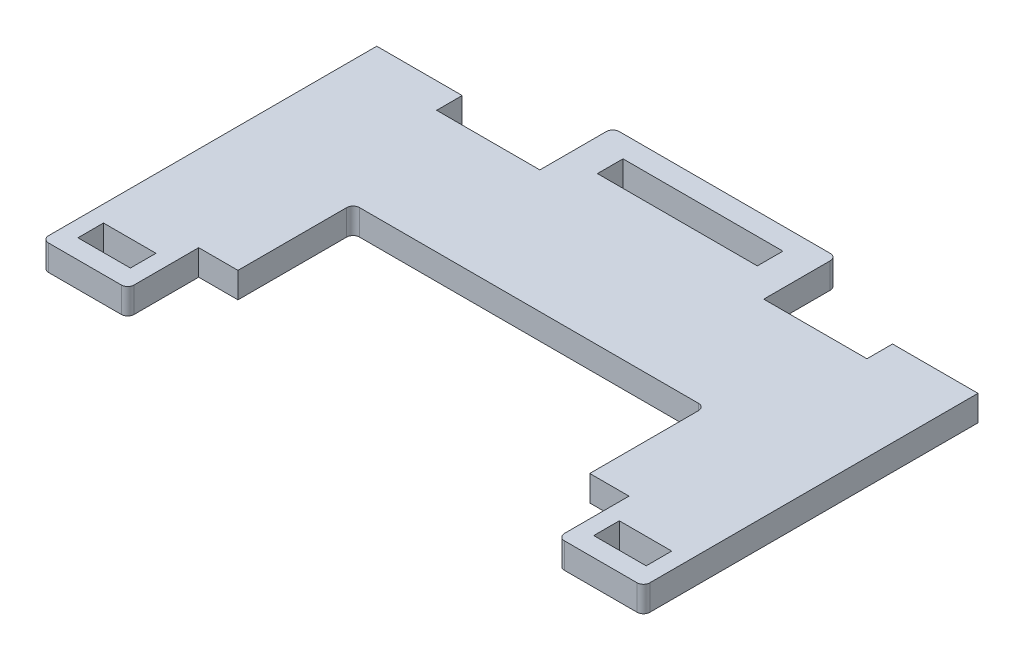
SolidWorks part; units mm, degrees
material "Oak"
ref_plane "Front Plane" through (0, 0, 0) normal (0, 0, 1) x (1, 0, 0)
ref_plane "Top Plane" through (0, 0, 0) normal (0, 1, 0) x (1, 0, 0)
ref_plane "Right Plane" through (0, 0, 0) normal (1, 0, 0) x (0, 0, -1)
sketch "Sketch1" plane through (0, 0, 0) normal (0, 1, 0) x (1, 0, 0)
  line L0 (0, 0) -> (0, 52.3)
  line L1 (0, 52.3) -> (13.36, 52.3)
  line L2 (13.36, 52.3) -> (13.36, 48.3)
  line L3 (13.36, 48.3) -> (29.5, 48.3)
  line L4 (29.5, 48.3) -> (29.5, 59.7)
  line L5 (29.5, 59.7) -> (47, 59.7)
  line L6 (47, 59.7) -> (47, 29.1)
  line L7 (47, 29.1) -> (19.5, 29.1)
  line L8 (19.5, 29.1) -> (19.5, 11.1)
  line L9 (19.5, 11.1) -> (13.36, 11.1)
  line L10 (13.36, 11.1) -> (13.36, 0)
  line L11 (13.36, 0) -> (0, 0)
  line L13 (2.58, 3) -> (10.78, 3)
  line L14 (2.58, 3) -> (2.58, 7)
  line L15 (2.58, 7) -> (10.78, 7)
  line L16 (10.78, 3) -> (10.78, 7)
  line L17 (47, 56.3) -> (34.5, 56.3)
  line L18 (47, 56.3) -> (47, 52.3)
  line L19 (47, 52.3) -> (34.5, 52.3)
  line L20 (34.5, 56.3) -> (34.5, 52.3)
  point P6 (6.68, 3)
  point P18 (6.68, 0)
  dimension "D1" = 47
  dimension "D2" = 52.3
  dimension "D3" = 4
  dimension "D4" = 13.36
  dimension "D5" = 27.5
  dimension "D6" = 11.1
  dimension "D7" = 18
  dimension "D8" = 17.5
  dimension "D9" = 11.4
  dimension "D10" = 8.2
  dimension "D11" = 4
  dimension "D12" = 3
  dimension "D13" = 5
  dimension "D14" = 4
  dimension "D15" = 3.4
extrude "Boss-Extrude1" add sketch "Sketch1" along normal blind 4 contours L20 L17 L6 L5 L4 L3 L2 L1 L0 L11 L10 L9 L8 L7 L19 L16 L13 L14 L15
fillet "Fillet1" radius 1 4 edges at (19.5, 2, -29.1) (13.36, 2, 0) (0, 2, 0) (29.5, 2, -59.7)
mirror "Mirror1" about plane through (47, 4, 0) normal (1, 0, 0) of "Boss-Extrude1", "Fillet1"
